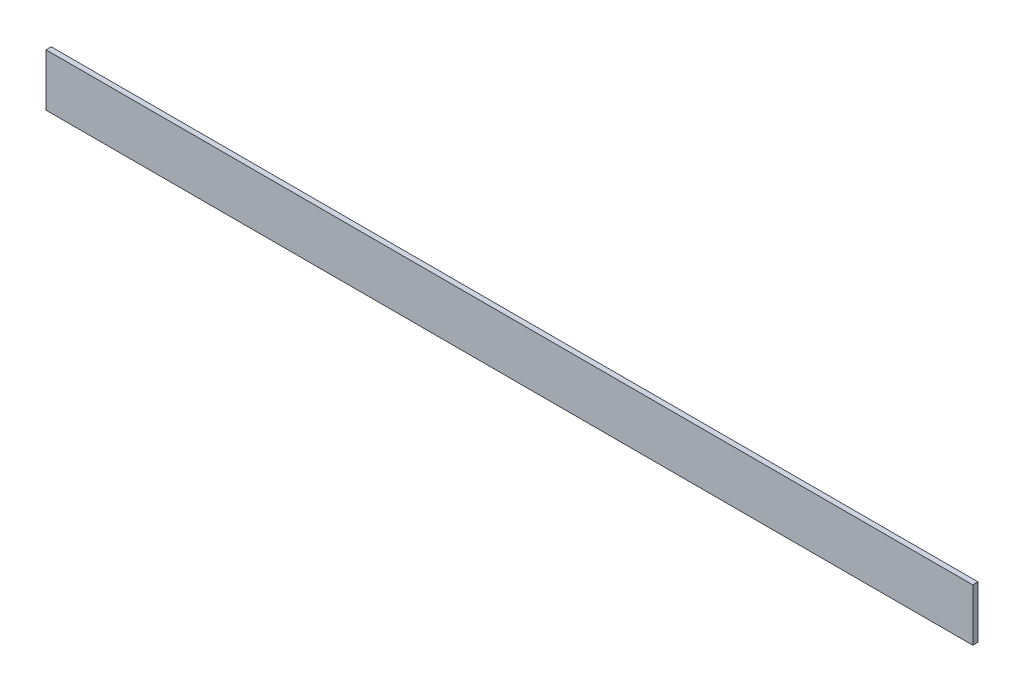
SolidWorks part; units mm, degrees
ref_plane "Front Plane" through (0, 0, 0) normal (0, 0, 1) x (1, 0, 0)
ref_plane "Top Plane" through (0, 0, 0) normal (0, 1, 0) x (1, 0, 0)
ref_plane "Right Plane" through (0, 0, 0) normal (1, 0, 0) x (0, 0, -1)
sketch "Sketch1" plane through (0, 0, 0) normal (0, 0, 1) x (1, 0, 0)
  line L0 (-177, 5.279) -> (177.485, 5.279)
  line L1 (-177, 5.279) -> (-177, -14.721)
  line L2 (-177, -14.721) -> (177.485, -14.721)
  line L3 (177.485, 5.279) -> (177.485, -14.721)
  dimension "D1" = 354.485
  dimension "D2" = 20
extrude "Boss-Extrude1" add sketch "Sketch1" along normal blind 2
